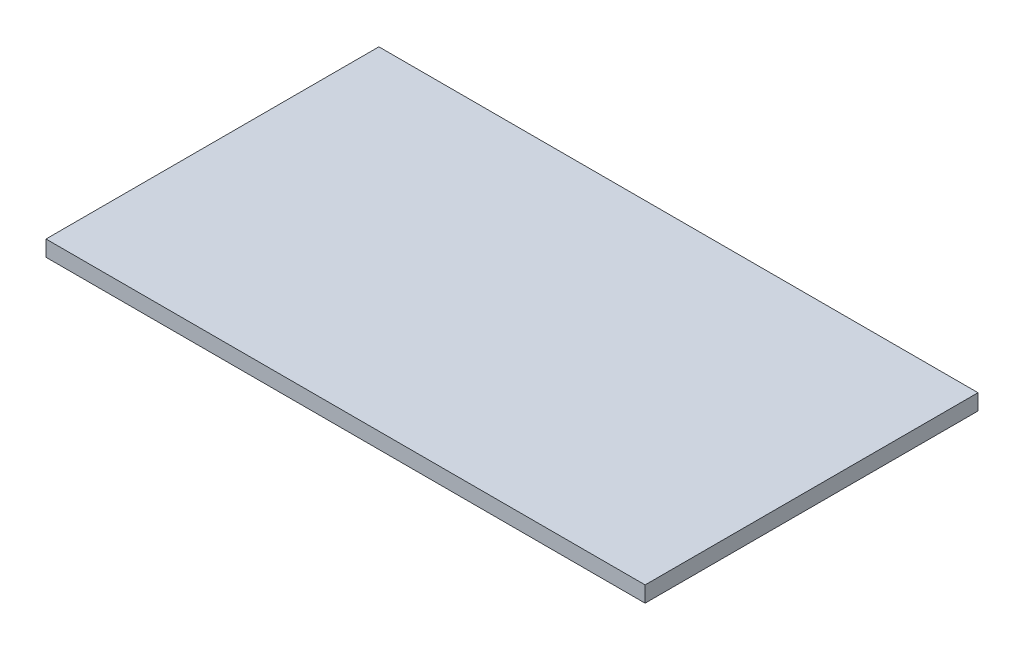
SolidWorks part; units mm, degrees
ref_plane "Front Plane" through (0, 0, 0) normal (0, 0, 1) x (1, 0, 0)
ref_plane "Top Plane" through (0, 0, 0) normal (0, 1, 0) x (1, 0, 0)
ref_plane "Right Plane" through (0, 0, 0) normal (1, 0, 0) x (0, 0, -1)
sketch "Sketch1" plane through (0, 0, 0) normal (0, 1, 0) x (1, 0, 0)
  line L1 (-28.7027, 18.165) -> (91.2973, 18.165)
  line L2 (-28.7027, 18.165) -> (-28.7027, -48.51)
  line L3 (-28.7027, -48.51) -> (91.2973, -48.51)
  line L4 (91.2973, 18.165) -> (91.2973, -48.51)
  dimension "D1" = 66.675
  dimension "D2" = 120
extrude "Boss-Extrude1" add sketch "Sketch1" along normal blind 3.175
